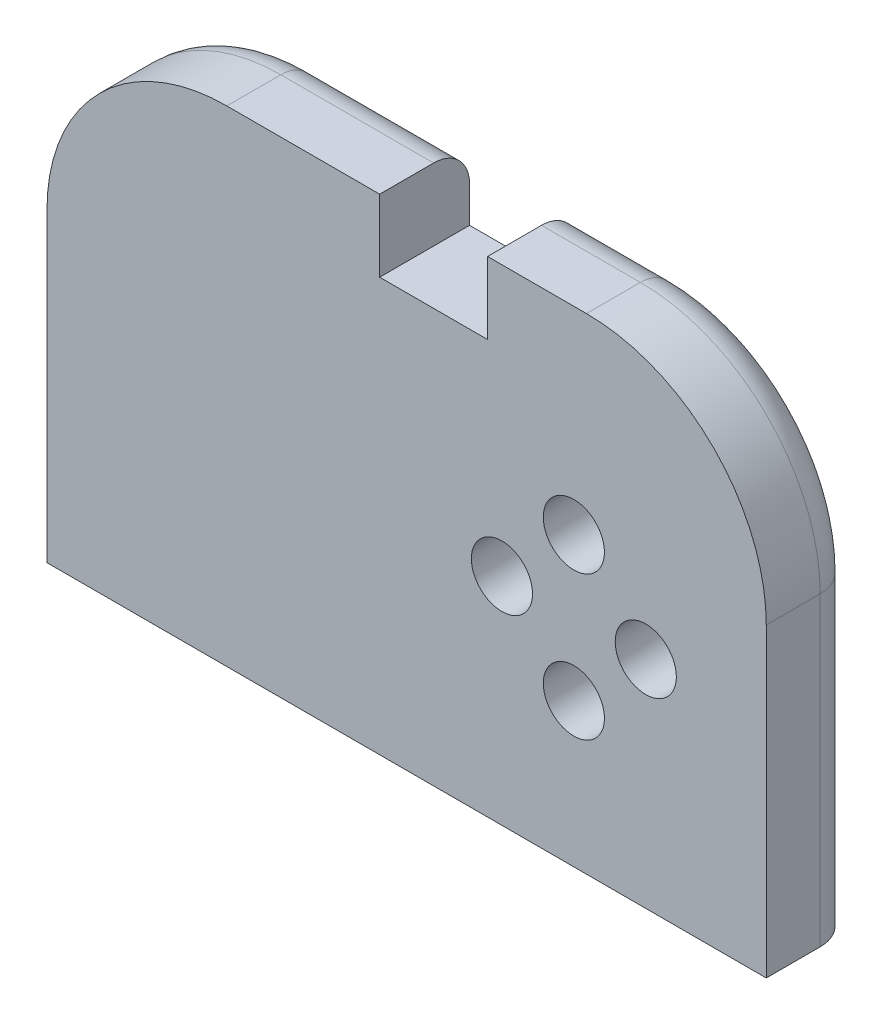
SolidWorks part; units mm, degrees
ref_plane "정면" through (0, 0, 0) normal (0, 0, 1) x (1, 0, 0)
ref_plane "윗면" through (0, 0, 0) normal (0, 1, 0) x (1, 0, 0)
ref_plane "우측면" through (0, 0, 0) normal (1, 0, 0) x (0, 0, -1)
sketch "스케치1" plane through (0, 0, 0) normal (0, 0, 1) x (1, 0, 0)
  line L0 (-1.5, 13.5) -> (-1.5, 9.5)
  line L1 (-20, 13.5) -> (-1.5, 13.5)
  line L2 (-20, 13.5) -> (-20, -13.5)
  line L3 (-20, -13.5) -> (20, -13.5)
  line L4 (20, 13.5) -> (20, -13.5)
  line L5 (-20, 13.5) -> (20, -13.5) construction
  line L6 (-20, -13.5) -> (20, 13.5) construction
  line L7 (-1.5, 9.5) -> (4.5, 9.5)
  line L8 (4.5, 9.5) -> (4.5, 13.5)
  line L9 (4.5, 13.5) -> (20, 13.5)
  point P0 (0, 0)
  dimension "D1" = 27
  dimension "D2" = 40
  dimension "D3" = 15.5
  dimension "D4" = 4
  dimension "D5" = 6
extrude "보스-돌출1" add sketch "스케치1" along normal blind 5
fillet "필렛1" radius 10 2 edges at (-20, 13.5, 2.5) (20, 13.5, 2.5)
fillet "필렛2" radius 2 6 edges at (-20, -5, 0) (-17.0711, 10.5711, 0) (7.25, 13.5, 0) (17.0711, 10.5711, 0) (-5.75, 13.5, 0) (20, -5, 0)
hole_wizard "M2 나사 구멍1" positions "스케치2" profile "스케치3" tap size "M2" standard "ISO"
sketch "스케치2" plane through (0, -13.5, 0) normal (0, -1, 0) x (-1, 0, 0)
  line L0 (20, -5) -> (20, -2) construction
  line L1 (18, 0) -> (-18, 0) construction
  point P0 (12.5, -3)
  point P2 (0, -3)
  point P4 (-12.5, -3)
  dimension "D1" = 7.5
  dimension "D2" = 12.5
  dimension "D3" = 12.5
  dimension "D4" = 3
cosmetic thread "구멍 나사산1" parameters "D1"=4.6, "D2"=2
cosmetic thread "구멍 나사산2" parameters "D1"=4.6, "D2"=2
cosmetic thread "구멍 나사산3" parameters "D1"=4.6, "D2"=2
sketch "스케치3" plane through (-12.5, -13.5, 3) normal (1, 0, 0) x (0, 0, -1)
  line L0 (0, 0) -> (0, 4.4807)
  line L1 (0, 4.4807) -> (0.8, 4)
  line L2 (0.8, 4) -> (0.8, 0)
  line L5 (0.8, 0) -> (0, 0)
  line L10 (0, 4.4807) -> (-0.8, 4) construction
  line L11 (0, -6.35) -> (0, 107.95) construction
  dimension "탭 드릴 지름" = 1.6
  dimension "탭 드릴 깊이" = 4
  dimension "드릴 각도" = 118
hole_wizard "M3 여유 구멍1" positions "스케치4" profile "스케치5" hole size "M3" standard "ISO"
sketch "스케치4" plane through (0, 0, 0) normal (0, 0, -1) x (-1, 0, 0)
  line L0 (-20, -13.5) -> (-20, 3.5) construction
  line L1 (18, -13.5) -> (-18, -13.5) construction
  circle A0 centre (-9.3, -1.5) radius 4 construction
  point P8 (-9.3, 2.5)
  point P10 (-5.3, -1.5)
  point P12 (-9.3, -5.5)
  point P14 (-13.3, -1.5)
  dimension "D2" = 8
  dimension "D1" = 10.7
  dimension "12" = 12
sketch "스케치5" plane through (13.3, -1.5, 0) normal (1, 0, 0) x (0, 1, 0)
  line L0 (0, 0) -> (0, 6.6215)
  line L1 (0, 6.6215) -> (1.7, 5.6)
  line L2 (1.7, 5.6) -> (1.7, 0)
  line L5 (1.7, 0) -> (0, 0)
  line L10 (0, 6.6215) -> (-1.7, 5.6) construction
  line L11 (0, -6.35) -> (0, 107.95) construction
  dimension "구멍 지름" = 3.4
  dimension "구멍 깊이" = 5.6
  dimension "드릴 각도" = 118
